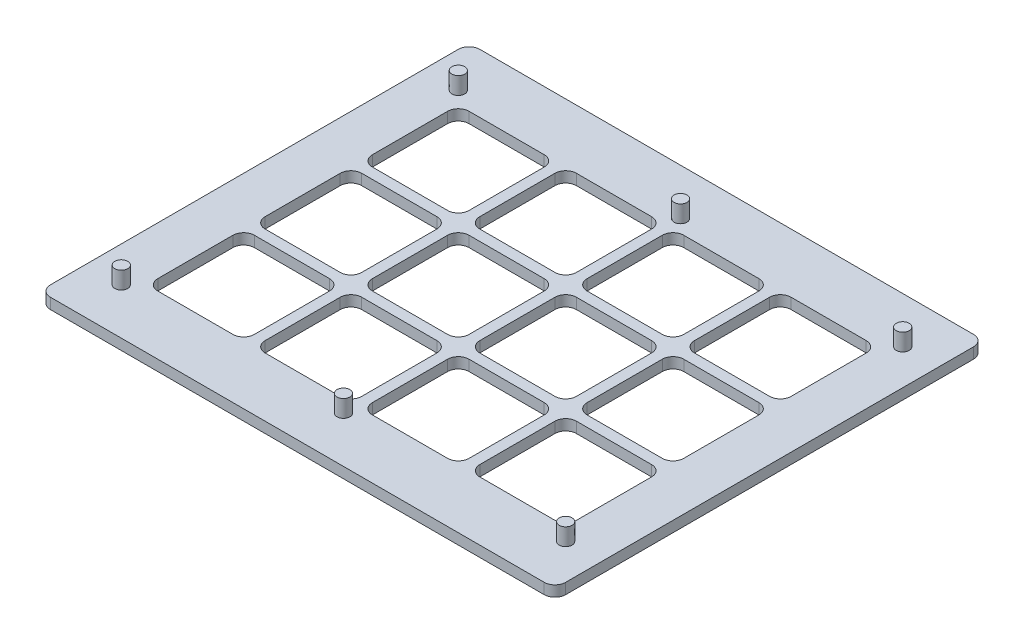
SolidWorks part; units mm, degrees
ref_plane "Front Plane" through (0, 0, 0) normal (0, 0, 1) x (1, 0, 0)
ref_plane "Top Plane" through (0, 0, 0) normal (0, 1, 0) x (1, 0, 0)
ref_plane "Right Plane" through (0, 0, 0) normal (1, 0, 0) x (0, 0, -1)
sketch "Sketch1" plane through (0, 0, 0) normal (0, 1, 0) x (1, 0, 0)
  line L1 (30.48, -25.4) -> (-30.48, -25.4)
  line L2 (30.48, -25.4) -> (30.48, 25.4)
  line L3 (30.48, 25.4) -> (-30.48, 25.4)
  line L4 (-30.48, -25.4) -> (-30.48, 25.4)
  line L5 (30.48, -25.4) -> (-30.48, 25.4) construction
  line L6 (30.48, 25.4) -> (-30.48, -25.4) construction
  point P0 (0, 0)
  dimension "D1" = 60.96
  dimension "D2" = 50.8
extrude "Boss-Extrude1" add sketch "Sketch1" along normal blind 1.27
sketch "Sketch2" plane through (0, 1.27, 0) normal (0, 1, 0) x (1, 0, 0)
  line L50 (-24.765, 12.7) -> (-30.48, 12.7) construction
  line L51 (-30.48, 25.4) -> (-30.48, -25.4) construction
  line L86 (-19.05, 18.415) -> (-19.05, 25.4) construction
  line L104 (30.48, 25.4) -> (-30.48, 25.4) construction
  line L105 (-24.765, 18.415) -> (-26.0113, 26.797) construction
  line L107 (-24.765, 18.415) -> (-31.8733, 20.955) construction
  line L110 (-24.765, 18.415) -> (-13.335, 18.415)
  line L111 (-24.765, 18.415) -> (-24.765, 6.985)
  line L112 (-24.765, 6.985) -> (-13.335, 6.985)
  line L113 (-13.335, 18.415) -> (-13.335, 6.985)
  point P69 (-29.1901, 21.59)
  dimension "D2" = 5.715
  dimension "D1" = 11.43
  dimension "D3" = 6.985
extrude "Cut-Extrude1" cut sketch "Sketch2" against normal through all
fillet "Fillet2" radius 1.27 4 edges at (-13.335, 0.635, -6.985) (-24.765, 0.635, -6.985) (-13.335, 0.635, -18.415) (-24.765, 0.635, -18.415)
sketch "Sketch4" plane through (0, 1.27, 0) normal (0, 1, 0) x (1, 0, 0)
  line L0 (-19.05, 18.415) -> (-19.05, 19.939) construction
  line L1 (-14.605, 18.415) -> (-23.495, 18.415) construction
  line L2 (-19.05, 19.939) -> (-26.289, 19.939) construction
  line L3 (-26.289, 19.939) -> (-26.289, 14.2065) construction
  line L8 (-26.289, 14.2065) -> (-24.765, 14.2065) construction
  line L9 (-24.765, 17.145) -> (-24.765, 8.255) construction
  circle A7 centre (-26.289, 19.939) radius 0.762
  dimension "D1" = 1.524
  dimension "D3" = 1.524
extrude "Boss-Extrude2" add sketch "Sketch4" along normal blind 2.032
fillet "Fillet3" radius 1.27 4 edges at (30.48, 0.635, 25.4) (-30.48, 0.635, 25.4) (-30.48, 0.635, -25.4) (30.48, 0.635, -25.4)
pattern_linear "LPattern13" count 4 spacing 12.7 along (1, 0, 0) count 3 spacing 12.7 along (0, 0, 1) of "Cut-Extrude1", "Fillet2"
pattern_linear "LPattern14" count 3 spacing 26.289 along (1, 0, 0) count 3 spacing 39.878 along (0, 0, 1) of "Boss-Extrude2"
